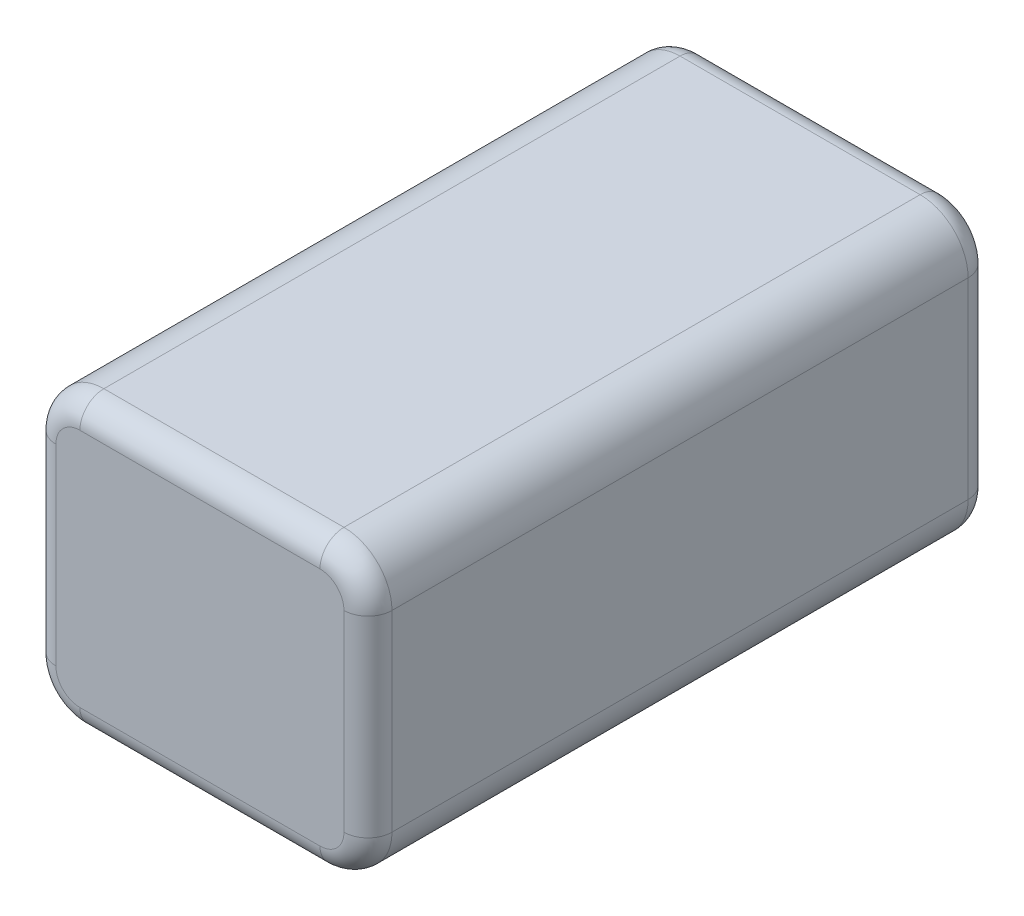
SolidWorks part; units mm, degrees
ref_plane "Front" through (0, 0, 0) normal (0, 0, 1) x (1, 0, 0)
ref_plane "Top" through (0, 0, 0) normal (0, 1, 0) x (1, 0, 0)
ref_plane "Right" through (0, 0, 0) normal (1, 0, 0) x (0, 0, -1)
sketch "Sketch1" plane through (0, 0, 0) normal (0, 0, 1) x (1, 0, 0)
  line L1 (-12.7, -15.24) -> (12.7, -15.24)
  line L2 (-17.78, -10.16) -> (-17.78, 10.16)
  line L3 (-12.7, 15.24) -> (12.7, 15.24)
  line L4 (17.78, -10.16) -> (17.78, 10.16)
  line L5 (-17.78, -15.24) -> (17.78, 15.24) construction
  line L6 (-17.78, 15.24) -> (17.78, -15.24) construction
  arc A0 (12.7, 15.24) -> (17.78, 10.16) centre (12.7, 10.16) cw
  arc A1 (12.7, -15.24) -> (17.78, -10.16) centre (12.7, -10.16) ccw
  arc A2 (-12.7, -15.24) -> (-17.78, -10.16) centre (-12.7, -10.16) cw
  arc A3 (-17.78, 10.16) -> (-12.7, 15.24) centre (-12.7, 10.16) cw
  point P0 (0, 0)
  dimension "D3" = 5.08
  dimension "D1" = 35.56
  dimension "D2" = 30.48
extrude "Boss-Extrude1" add sketch "Sketch1" along normal mid plane 66.04
fillet "Fillet1" radius 2.54 16 edges at (0, 15.24, -33.02) (-16.2921, 13.7521, -33.02) (-17.78, 0, -33.02) (-16.2921, -13.7521, -33.02) (0, -15.24, -33.02) (16.2921, -13.7521, -33.02) (17.78, 0, -33.02) (16.2921, 13.7521, -33.02) (17.78, 0, 33.02) (16.2921, -13.7521, 33.02) (0, -15.24, 33.02) (-16.2921, -13.7521, 33.02) (-17.78, 0, 33.02) (-16.2921, 13.7521, 33.02) (0, 15.24, 33.02) (16.2921, 13.7521, 33.02)
